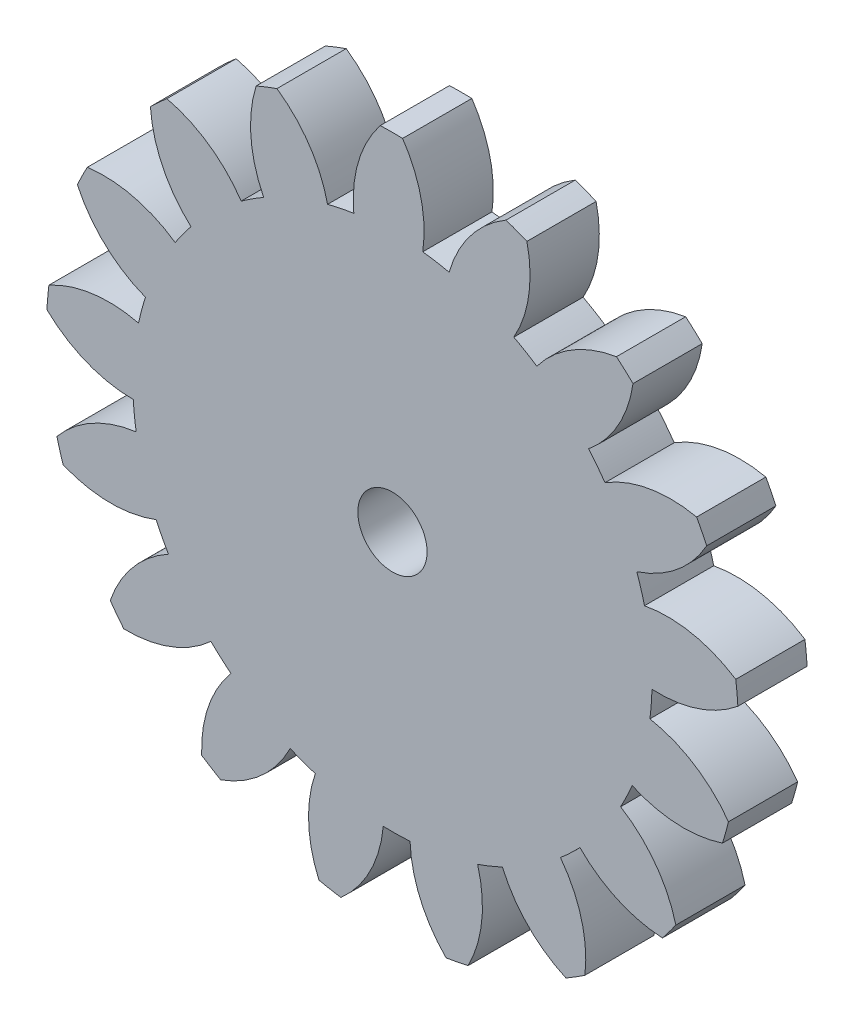
SolidWorks part; units mm, degrees
ref_plane "Ebene vorne" through (0, 0, 0) normal (0, 0, 1) x (1, 0, 0)
ref_plane "Ebene oben" through (0, 0, 0) normal (0, 1, 0) x (1, 0, 0)
ref_plane "Ebene rechts" through (0, 0, 0) normal (1, 0, 0) x (0, 0, -1)
sketch "Skizze1" plane through (0, 0, 0) normal (0, 0, 1) x (1, 0, 0)
  circle A0 centre (0, 0) radius 20
  dimension "D1" = 40
extrude "Aufsatz-Linear austragen1" add sketch "Skizze1" along normal blind 4
sketch "Skizze2" plane through (0, 0, 4) normal (0, 0, 1) x (1, 0, 0)
  circle A0 centre (0, 0) radius 2
  dimension "D1" = 4
extrude "Schnitt-Linear austragen1" cut sketch "Skizze2" against normal up to next
sketch "Skizze3" plane through (0, 0, 4) normal (0, 0, 1) x (1, 0, 0)
  circle A0 centre (0, 0) radius 15 construction
  arc A1 (0.5868, 19.9914) -> (1.7512, 14.8974) centre (-5.3715, 15.9493) cw
  circle A2 centre (0, 0) radius 20 construction
  arc A3 (3.2753, 14.638) -> (6.5622, 18.8928) centre (10.2045, 12.682) cw
  arc A4 (0.5868, 19.9914) -> (6.5622, 18.8928) centre (0, 0) cw
  arc A5 (1.7512, 14.8974) -> (3.2753, 14.638) centre (0, 0) cw
  point P12 (6.5622, 18.8928)
  dimension "D1" = 30
extrude "Schnitt-Linear austragen2" cut sketch "Skizze3" against normal up to next (4 mm away)
pattern_circular "Kreismuster1" count 17 over 360 about axis through (0, 0, 0) along (0, 0, 1) of "Schnitt-Linear austragen2"
